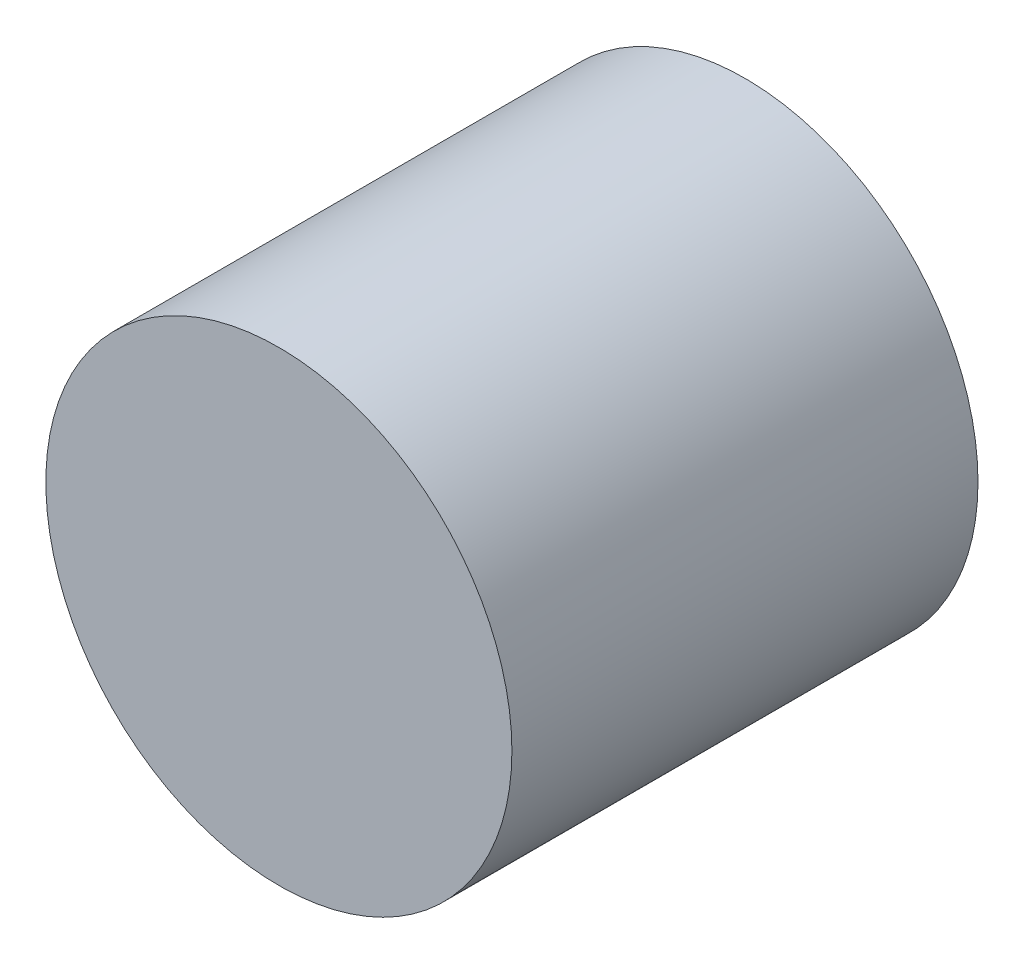
SolidWorks part; units mm, degrees
ref_plane "Plan de face" through (0, 0, 0) normal (0, 0, 1) x (1, 0, 0)
ref_plane "Plan de dessus" through (0, 0, 0) normal (0, 1, 0) x (1, 0, 0)
ref_plane "Plan de droite" through (0, 0, 0) normal (1, 0, 0) x (0, 0, -1)
sketch "Esquisse1" plane through (0, 0, 0) normal (0, 0, 1) x (1, 0, 0)
  circle A0 centre (0, 0) radius 29
extrude "Boss.-Extru.1" add sketch "Esquisse1" along normal blind 58
